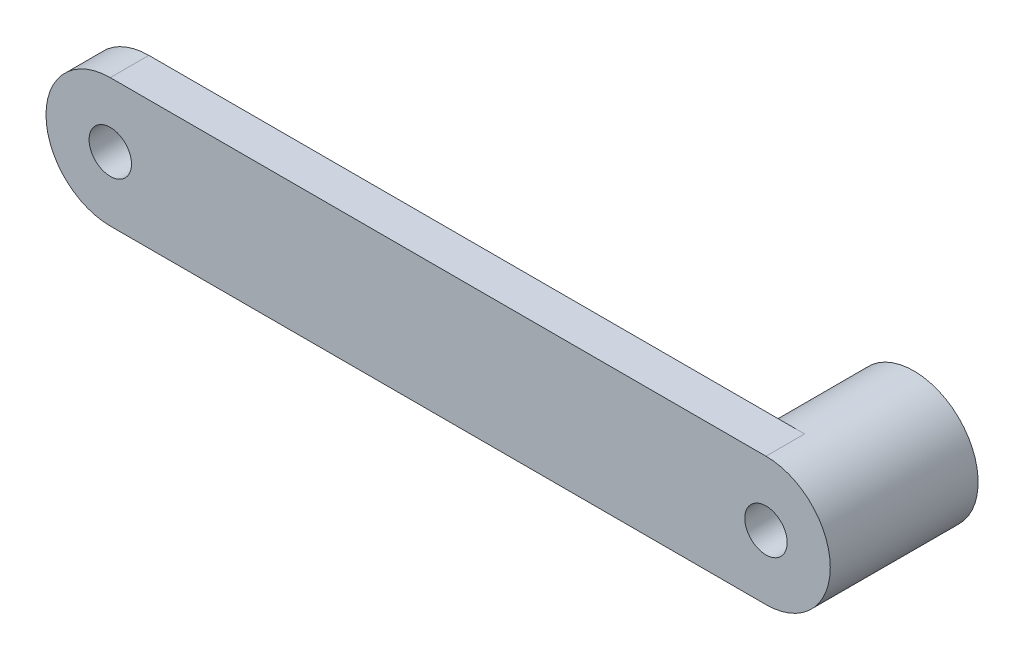
SolidWorks part; units mm, degrees
ref_plane "前基準面" through (0, 0, 0) normal (0, 0, 1) x (1, 0, 0)
ref_plane "上基準面" through (0, 0, 0) normal (0, 1, 0) x (1, 0, 0)
ref_plane "右基準面" through (0, 0, 0) normal (1, 0, 0) x (0, 0, -1)
sketch "草圖1" plane through (0, 0, 0) normal (0, 0, 1) x (1, 0, 0)
  line L0 (0, 0) -> (51, 0) construction
  line L1 (0, 5) -> (51, 5)
  line L2 (0, -5) -> (51, -5)
  circle A0 centre (0, 0) radius 1.65
  circle A1 centre (51, 0) radius 1.65
  arc A2 (0, 5) -> (0, -5) centre (0, 0) ccw
  arc A3 (51, -5) -> (51, 5) centre (51, 0) ccw
  point P5 (25.5, 0)
  dimension "D3" = 3.3
  dimension "D1" = 51
  dimension "D2" = 10
extrude "填料-伸長1" add sketch "草圖1" along normal blind 3
sketch "草圖2" plane through (0, 0, 0) normal (0, 0, -1) x (-1, 0, 0)
  circle A0 centre (-51, 0) radius 5
  circle A1 centre (-51, 0) radius 1.65
  circle A2 centre (-51, 0) radius 1.65 construction
extrude "填料-伸長2" add sketch "草圖2" along normal blind 8.5
